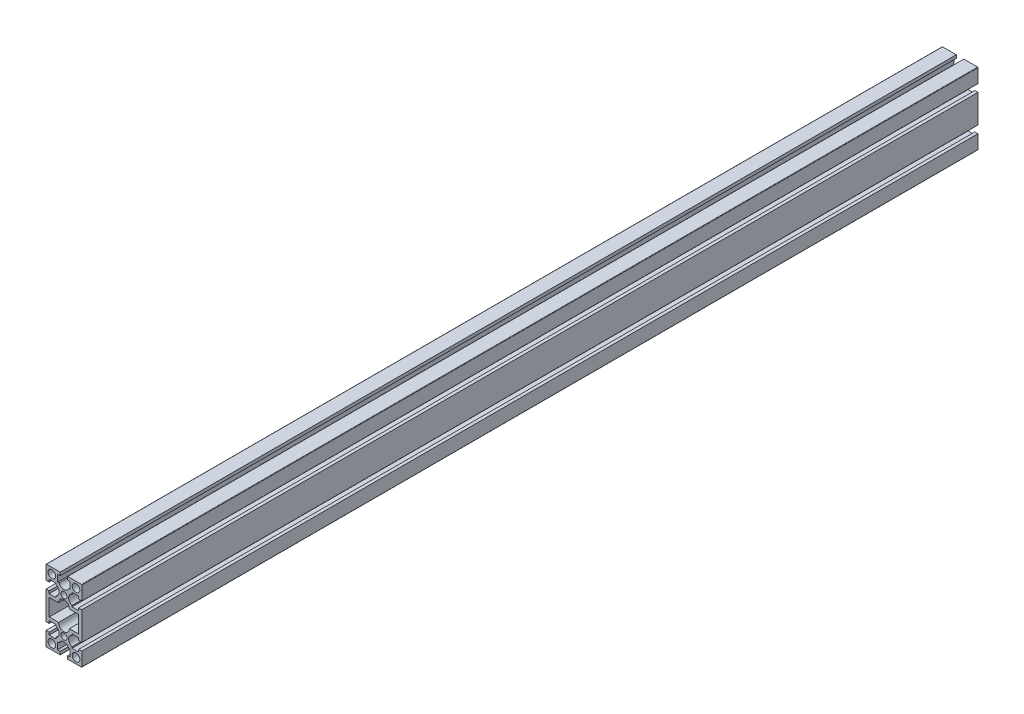
SolidWorks part; units mm, degrees
material "6063 T5"
ref_plane "Спереди" through (0, 0, 0) normal (0, 0, 1) x (1, 0, 0)
ref_plane "Сверху" through (0, 0, 0) normal (0, 1, 0) x (1, 0, 0)
ref_plane "Справа" through (0, 0, 0) normal (1, 0, 0) x (0, 0, -1)
sketch "Эскиз1" plane through (0, 0, 0) normal (0, 0, 1) x (1, 0, 0)
  line L0 (11.3549, 30.3863) -> (41.3549, 30.3863) construction
  line L10 (-20, 0) -> (20, 0) construction
  line L11 (-20, 7) -> (-20, 19.5)
  line L12 (-19.5, 20) -> (-3.4, 20)
  line L14 (7, 20) -> (19.5, 20)
  line L15 (20, 19.5) -> (20, 3.4)
  line L16 (0, 0) -> (0, -40) construction
  line L17 (0, -20) -> (26.4225, -20) construction
  line L18 (13.5, -53.5) -> (-13.5, -26.5) construction
  line L19 (13.5, -26.5) -> (-13.5, -53.5) construction
  line L20 (-20.0402, 23.0813) -> (19.9598, 23.0813) construction
  line L21 (13.5, -13.5) -> (-13.5, -13.5) construction
  line L22 (13.5, -13.5) -> (13.5, 13.5) construction
  line L23 (13.5, 13.5) -> (-13.5, 13.5) construction
  line L24 (-13.5, -13.5) -> (-13.5, 13.5) construction
  line L25 (13.5, -13.5) -> (-13.5, 13.5) construction
  line L26 (13.5, 13.5) -> (-13.5, -13.5) construction
  line L27 (-13.5, -26.5) -> (-13.5, -53.5) construction
  line L28 (13.5, -53.5) -> (-13.5, -53.5) construction
  line L29 (13.5, -26.5) -> (13.5, -53.5) construction
  line L30 (13.5, -26.5) -> (-13.5, -26.5) construction
  line L31 (-20, -40) -> (20, -40) construction
  line L32 (20, -59.5) -> (20, -43.4)
  line L33 (7, -60) -> (19.5, -60)
  line L34 (-19.5, -60) -> (-3.4, -60)
  line L35 (-20, -47) -> (-20, -59.5)
  line L36 (-20, -7) -> (-20, -33)
  line L37 (20, -7) -> (20, -33)
  line L38 (-28.6566, 20.0565) -> (-28.6566, -59.9435) construction
  line L39 (16.4, -29.5) -> (16.4, -10.5)
  line L40 (16.4, -10.5) -> (6, -10.5)
  line L41 (-16.4, -10.5) -> (-6, -10.5)
  line L42 (-16.4, -29.5) -> (-16.4, -10.5)
  line L43 (-16.4, -29.5) -> (-6, -29.5)
  line L44 (16.4, -29.5) -> (6, -29.5)
  circle A0 centre (-13.5, 13.5) radius 4.25
  circle A1 centre (13.5, 13.5) radius 4.25
  circle A4 centre (0, 0) radius 3.4
  arc A5 (-20, -59.5) -> (-19.5, -60) centre (-19.5, -59.5) ccw
  arc A6 (19.5, -60) -> (20, -59.5) centre (19.5, -59.5) ccw
  arc A7 (19.5, 20) -> (20, 19.5) centre (19.5, 19.5) cw
  arc A8 (-20, 19.5) -> (-19.5, 20) centre (-19.5, 19.5) cw
  circle A9 centre (0, -40) radius 3.4
  circle A10 centre (13.5, -53.5) radius 4.25
  circle A11 centre (-13.5, -53.5) radius 4.25
  arc A12 (6, -10.5) -> (-6, -10.5) centre (0, -10.5) ccw
  arc A13 (6, -29.5) -> (-6, -29.5) centre (0, -29.5) cw
  point P4 (0, 0)
  point P17 (0, 0)
  point P49 (0, -40)
  point P50 (0, -40)
  point P71 (-16.4, -20)
  point P72 (16.4, -20)
  line B0 (-20, 7) -> (-20, 4.2)
  line B1 (-20, 4.2) -> (-16.5, 4.2)
  line B2 (-16.5, 4.2) -> (-16.5, 7)
  line B3 (-16.5, 7) -> (-9, 7)
  line B4 (-9, -7) -> (-16.5, -7)
  line B5 (-16.5, -7) -> (-16.5, -4.2)
  line B6 (-16.5, -4.2) -> (-20, -4.2)
  line B7 (-20, -4.2) -> (-20, -7)
  line B8 (-20, 7) -> (-20, -7) construction
  line B9 (-9, 7) -> (-9, 5.5417)
  line B10 (-9, -7) -> (-9, -5.5417)
  arc B11 (-9, 5.5417) -> (-9, -5.5417) centre (-11.3, 0) cw
  line B12 (7, 20) -> (4.2, 20)
  line B13 (4.2, 20) -> (4.2, 16.5)
  line B14 (4.2, 16.5) -> (7, 16.5)
  line B15 (7, 16.5) -> (7, 9)
  line B16 (-7, 9) -> (-7, 16.5)
  line B17 (-7, 16.5) -> (-4.2, 16.5)
  line B18 (-4.2, 16.5) -> (-4.2, 20)
  line B19 (-4.2, 20) -> (-7, 20)
  line B20 (7, 20) -> (-7, 20) construction
  line B21 (7, 9) -> (5.5417, 9)
  line B22 (-7, 9) -> (-5.5417, 9)
  arc B23 (5.5417, 9) -> (-5.5417, 9) centre (0, 11.3) cw
  line B24 (20, -7) -> (20, -4.2)
  line B25 (20, -4.2) -> (16.5, -4.2)
  line B26 (16.5, -4.2) -> (16.5, -7)
  line B27 (16.5, -7) -> (9, -7)
  line B28 (9, 7) -> (16.5, 7)
  line B29 (16.5, 7) -> (16.5, 4.2)
  line B30 (16.5, 4.2) -> (20, 4.2)
  line B31 (20, 4.2) -> (20, 7)
  line B32 (20, -7) -> (20, 7) construction
  line B33 (9, -7) -> (9, -5.5417)
  line B34 (9, 7) -> (9, 5.5417)
  arc B35 (9, -5.5417) -> (9, 5.5417) centre (11.3, 0) cw
  line B36 (20, -33) -> (20, -35.8)
  line B37 (20, -35.8) -> (16.5, -35.8)
  line B38 (16.5, -35.8) -> (16.5, -33)
  line B39 (16.5, -33) -> (9, -33)
  line B40 (9, -47) -> (16.5, -47)
  line B41 (16.5, -47) -> (16.5, -44.2)
  line B42 (16.5, -44.2) -> (20, -44.2)
  line B43 (20, -44.2) -> (20, -47)
  line B44 (20, -33) -> (20, -47) construction
  line B45 (9, -33) -> (9, -34.4583)
  line B46 (9, -47) -> (9, -45.5417)
  arc B47 (9, -34.4583) -> (9, -45.5417) centre (11.3, -40) ccw
  line B48 (-20, -47) -> (-20, -44.2)
  line B49 (-20, -44.2) -> (-16.5, -44.2)
  line B50 (-16.5, -44.2) -> (-16.5, -47)
  line B51 (-16.5, -47) -> (-9, -47)
  line B52 (-9, -33) -> (-16.5, -33)
  line B53 (-16.5, -33) -> (-16.5, -35.8)
  line B54 (-16.5, -35.8) -> (-20, -35.8)
  line B55 (-20, -35.8) -> (-20, -33)
  line B56 (-20, -47) -> (-20, -33) construction
  line B57 (-9, -47) -> (-9, -45.5417)
  line B58 (-9, -33) -> (-9, -34.4583)
  arc B59 (-9, -45.5417) -> (-9, -34.4583) centre (-11.3, -40) ccw
  line B60 (7, -60) -> (4.2, -60)
  line B61 (4.2, -60) -> (4.2, -56.5)
  line B62 (4.2, -56.5) -> (7, -56.5)
  line B63 (7, -56.5) -> (7, -49)
  line B64 (-7, -49) -> (-7, -56.5)
  line B65 (-7, -56.5) -> (-4.2, -56.5)
  line B66 (-4.2, -56.5) -> (-4.2, -60)
  line B67 (-4.2, -60) -> (-7, -60)
  line B68 (7, -60) -> (-7, -60) construction
  line B69 (7, -49) -> (5.5417, -49)
  line B70 (-7, -49) -> (-5.5417, -49)
  arc B71 (5.5417, -49) -> (-5.5417, -49) centre (0, -51.3) ccw
  dimension "D5" = 8.5
  dimension "D6" = 6.8
  dimension "D8" = 0.5
  dimension "D14" = 6
  dimension "D1" = 30
  dimension "D2" = 40
  dimension "D3" = 4
  dimension "D4" = 27
  dimension "D7" = 40
  dimension "D9" = 40
  dimension "D10" = 80
  dimension "D11" = 80
  dimension "D12" = 9.5
  dimension "D13" = 3.6
sketch_block_instance "Блок1-1"
sketch_block "Блок1" parameters "D4"=6.5, "D1"=14, "D2"=8.4, "D3"=2.2, "D5"=6, "D6"=1.3698
sketch_block_instance "Блок1-2"
sketch_block_instance "Блок1-3"
sketch_block_instance "Блок1-6"
sketch_block_instance "Блок1-10"
sketch_block_instance "Блок1-11"
sketch_block_instance "Блок1-12"
extrude "Бобышка-Вытянуть1" add sketch "Эскиз1" along normal blind 1000
